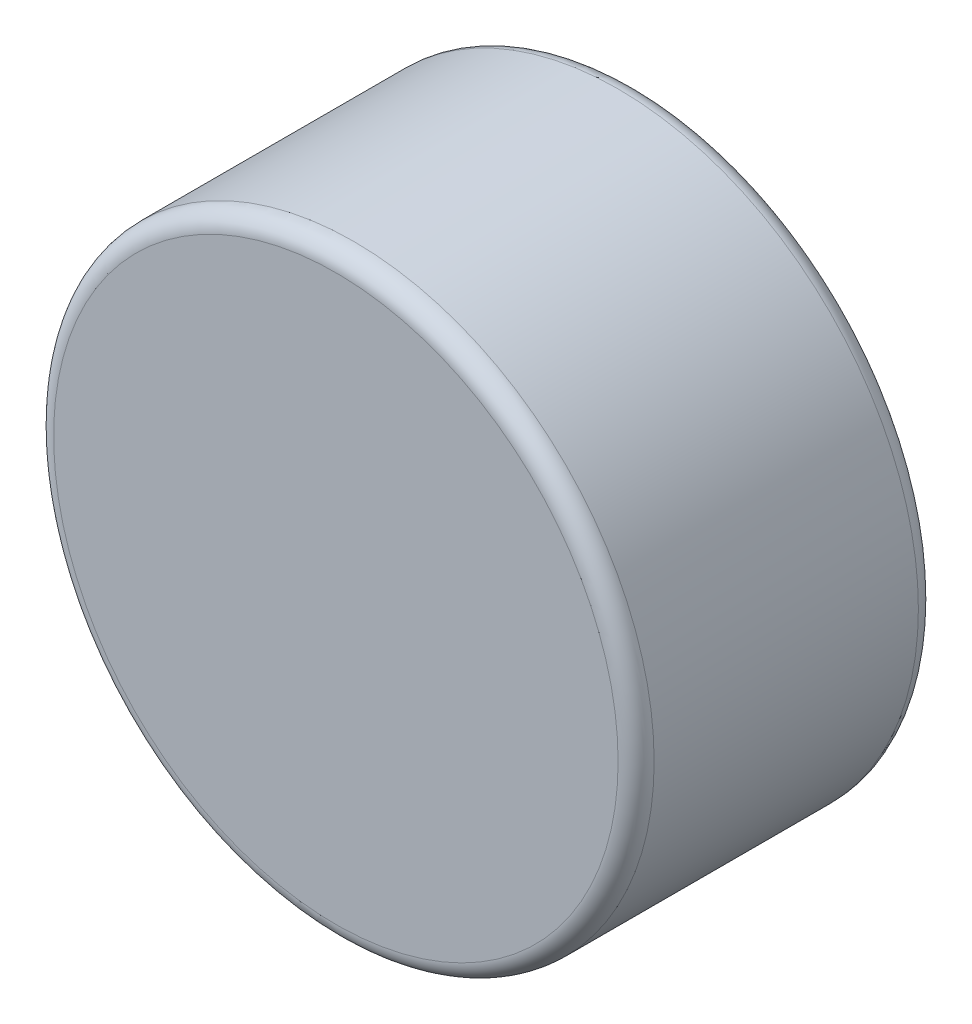
SolidWorks part; units mm, degrees
ref_plane "Front Plane" through (0, 0, 0) normal (0, 0, 1) x (1, 0, 0)
ref_plane "Top Plane" through (0, 0, 0) normal (0, 1, 0) x (1, 0, 0)
ref_plane "Right Plane" through (0, 0, 0) normal (1, 0, 0) x (0, 0, -1)
sketch "Sketch1" plane through (0, 0, 0) normal (0, 0, 1) x (1, 0, 0)
  circle A0 centre (0, 0) radius 5
  dimension "D1" = 10
extrude "Boss-Extrude1" add sketch "Sketch1" along normal blind 5
fillet "Fillet1" radius 0.3 2 edges at (5, 0, 5) (5, 0, 0)
